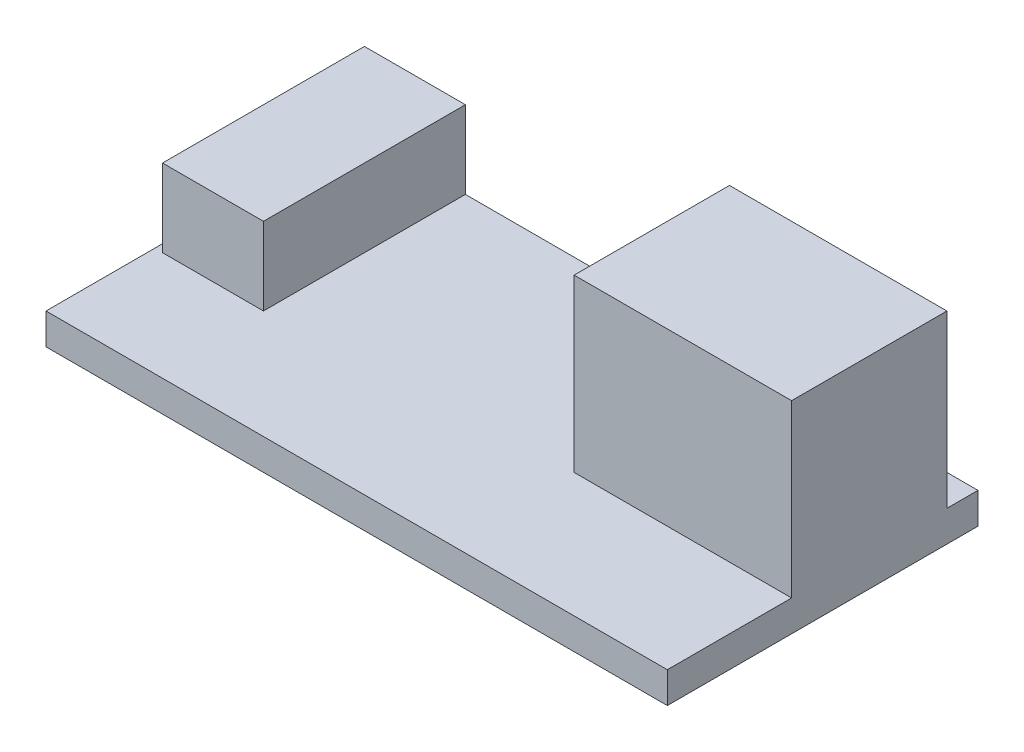
SolidWorks part; units mm, degrees
ref_plane "Front Plane" through (0, 0, 0) normal (0, 0, 1) x (1, 0, 0)
ref_plane "Top Plane" through (0, 0, 0) normal (0, 1, 0) x (1, 0, 0)
ref_plane "Right Plane" through (0, 0, 0) normal (1, 0, 0) x (0, 0, -1)
sketch "Sketch1" plane through (0, 0, 0) normal (0, 1, 0) x (1, 0, 0)
  line L1 (-20, -10) -> (20, -10)
  line L2 (-20, -10) -> (-20, 10)
  line L3 (-20, 10) -> (20, 10)
  line L4 (20, -10) -> (20, 10)
  line L5 (-20, -10) -> (20, 10) construction
  line L6 (-20, 10) -> (20, -10) construction
  point P0 (0, 0)
  dimension "D1" = 20
  dimension "D2" = 40
extrude "Boss-Extrude1" add sketch "Sketch1" along normal blind 2
sketch "Sketch2" plane through (0, 2, 0) normal (0, 1, 0) x (1, 0, 0)
  line L0 (20, -10) -> (20, 10) construction
  line L1 (6, -2) -> (20, -2)
  line L2 (6, -2) -> (6, 8)
  line L3 (6, 8) -> (20, 8)
  line L4 (20, -2) -> (20, 8)
  line L5 (20, 10) -> (-20, 10) construction
  dimension "D1" = 14
  dimension "D2" = 10
  dimension "D3" = 2
extrude "Boss-Extrude2" add sketch "Sketch2" along normal blind 11
sketch "Sketch3" plane through (0, 2, 0) normal (0, 1, 0) x (1, 0, 0)
  line L0 (20, 10) -> (-20, 10) construction
  line L1 (-19.5, 10) -> (-13, 10)
  line L2 (-19.5, 10) -> (-19.5, -3)
  line L3 (-19.5, -3) -> (-13, -3)
  line L4 (-13, 10) -> (-13, -3)
  line L5 (-20, 10) -> (-20, -10) construction
  dimension "D1" = 13
  dimension "D2" = 6.5
  dimension "D3" = 0.5
extrude "Boss-Extrude3" add sketch "Sketch3" along normal blind 5
